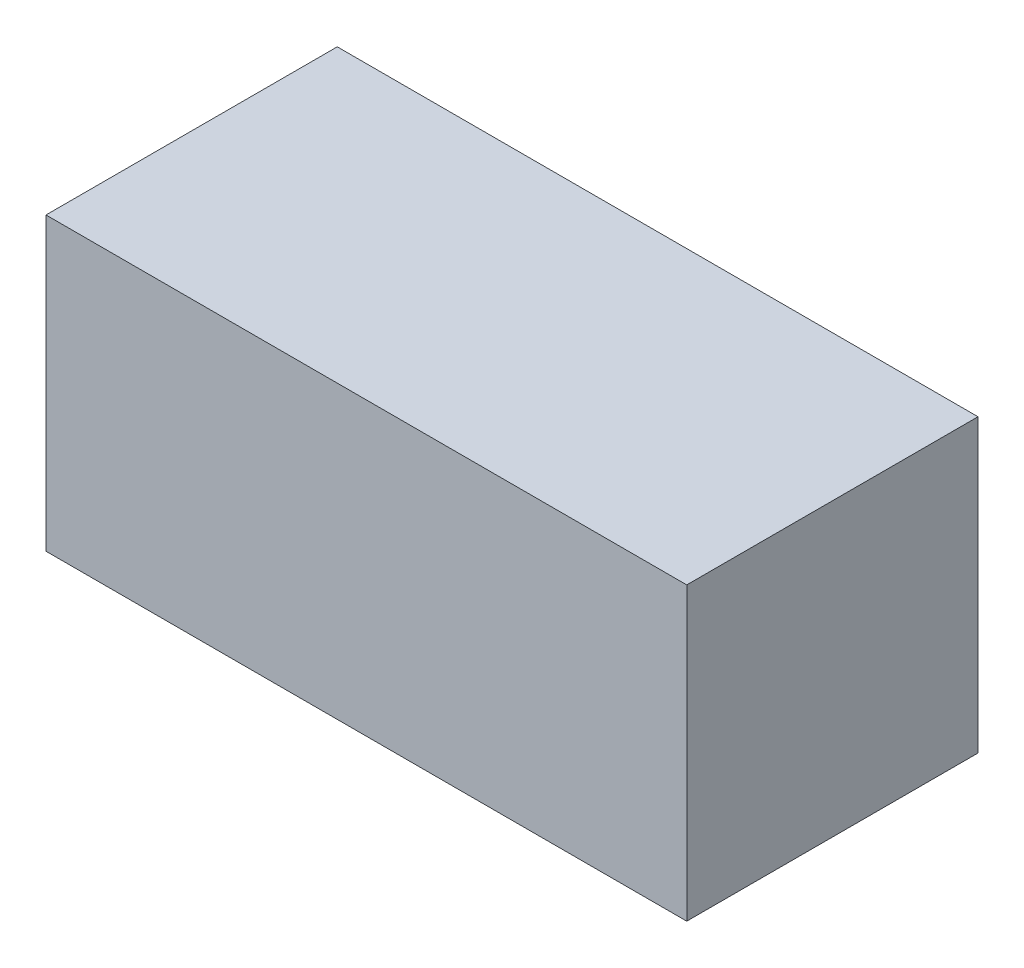
SolidWorks part; units mm, degrees
material "Custom Plastic"
ref_plane "X-Y Datum" through (0, 0, 0) normal (0, 0, 1) x (1, 0, 0)
ref_plane "X-Z Datum" through (0, 0, 0) normal (0, 1, 0) x (1, 0, 0)
ref_plane "Y-Z Datum" through (0, 0, 0) normal (1, 0, 0) x (0, 0, -1)
sketch "Sketch1" plane through (0, 0, 0) normal (0, 0, 1) x (1, 0, 0)
  line L1 (-83.82, 38.1) -> (83.82, 38.1)
  line L2 (-83.82, 38.1) -> (-83.82, -38.1)
  line L3 (-83.82, -38.1) -> (83.82, -38.1)
  line L4 (83.82, 38.1) -> (83.82, -38.1)
  line L5 (-83.82, 38.1) -> (83.82, -38.1) construction
  line L6 (-83.82, -38.1) -> (83.82, 38.1) construction
  point P0 (0, 0)
  dimension "D1" = 167.64
  dimension "D2" = 76.2
extrude "Boss-Extrude1" add sketch "Sketch1" along normal blind 76.2
